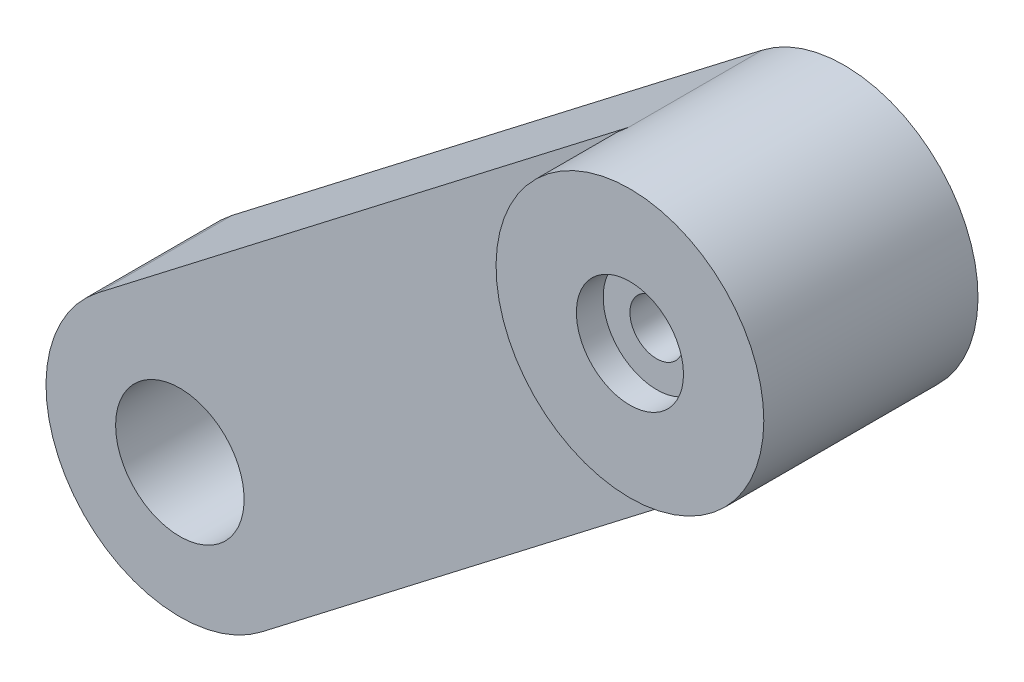
SolidWorks part; units mm, degrees
ref_plane "Front Plane" through (0, 0, 0) normal (0, 0, 1) x (1, 0, 0)
ref_plane "Top Plane" through (0, 0, 0) normal (0, 1, 0) x (1, 0, 0)
ref_plane "Right Plane" through (0, 0, 0) normal (1, 0, 0) x (0, 0, -1)
sketch "Sketch1" plane through (0, 0, 0) normal (0, 0, 1) x (0.9998, -0.022, 0)
  line L0 (-41.8829, 111.4723) -> (-17.0715, 91.626) construction
  line L1 (-1.7639, 79.3817) -> (-1.7639, 99.3817) construction
  line L2 (-1.7639, 99.3817) -> (-51.7712, 99.3817) construction
  line L3 (-46.2352, 83.6971) -> (-26.7675, 99.3817) construction
  line L4 (-46.2352, 83.6971) -> (-49.3722, 87.5906) construction
  line L5 (-49.3722, 87.5906) -> (-43.0983, 79.8035) construction
  line L6 (-49.3722, 87.5906) -> (-29.9044, 103.2753)
  line L7 (-43.0983, 79.8035) -> (-23.6306, 95.4882)
  line L8 (-29.9044, 103.2753) -> (-23.6306, 95.4882) construction
  circle A0 centre (-1.7639, 79.3817) radius 2.5 construction
  circle A1 centre (-1.7639, 79.3817) radius 2.5 construction
  circle A3 centre (-26.7675, 99.3817) radius 2.4
  arc A4 (-22.8629, 96.2585) -> (-30.6611, 96.2448) centre (-26.7675, 99.3817) ccw
  circle A6 centre (-46.2352, 83.6971) radius 1.5 construction
  arc A7 (-49.3722, 87.5906) -> (-43.0983, 79.8035) centre (-46.2352, 83.6971) ccw
  arc A8 (-23.6306, 95.4882) -> (-29.9044, 103.2753) centre (-26.7675, 99.3817) ccw
  point P18 (-26.7675, 99.3817)
  dimension "D1" = 5
  dimension "D2" = 5
  dimension "D4" = 4.8
  dimension "D5" = 3
  dimension "D6" = 10
  dimension "D3" = 20
  dimension "D7" = 25
extrude "Boss-Extrude1" add sketch "Sketch1" along normal blind 5
sketch "Sketch2" plane through (0, 0, 0) normal (0, 0, -1) x (-1, 0, 0)
  circle A0 centre (44.3801, 84.6953) radius 2.4
  dimension "D1" = 4.8
extrude "Cut-Extrude1" cut sketch "Sketch2" against normal blind 5
sketch "Sketch4" plane through (0, 0, 0) normal (0, 0, -1) x (-1, 0, 0)
  line L0 (44.3801, 84.6953) -> (41.2108, 87.1357) construction
  line L1 (42.4785, 86.1595) -> (39.1522, 88.7207) construction
  line L2 (38.2371, 87.5322) -> (40.0673, 89.9092)
  line L3 (41.2108, 87.1357) -> (40.0673, 89.9092)
  line L4 (38.2371, 87.5322) -> (41.2108, 87.1357)
  line L5 (47.4305, 88.6571) -> (27.622, 103.909) construction
  circle A0 centre (44.3801, 84.6953) radius 2.4 construction
  point P10 (39.1522, 88.7207)
  dimension "D1" = 3
  dimension "D2" = 3
  dimension "D3" = 4
  dimension "D4" = 3
extrude "Cut-Extrude2" cut sketch "Sketch4" against normal blind 1
sketch "Sketch5" plane through (0, 0, 5) normal (0, 0, 1) x (1, 0, 0)
  circle A0 centre (-24.5716, 99.9473) radius 5
  circle A1 centre (-24.5716, 99.9473) radius 1
  dimension "D1" = 10
  dimension "D2" = 2
extrude "Boss-Extrude2" add sketch "Sketch5" along normal blind 3
sketch "Sketch6" plane through (0, 0, 8) normal (0, 0, 1) x (1, 0, 0)
  circle A0 centre (-24.5716, 99.9473) radius 2
extrude "Cut-Extrude3" cut sketch "Sketch6" against normal offset from surface (1 mm away) 2 up to face at (-36.4567, 90.7961, 5)
